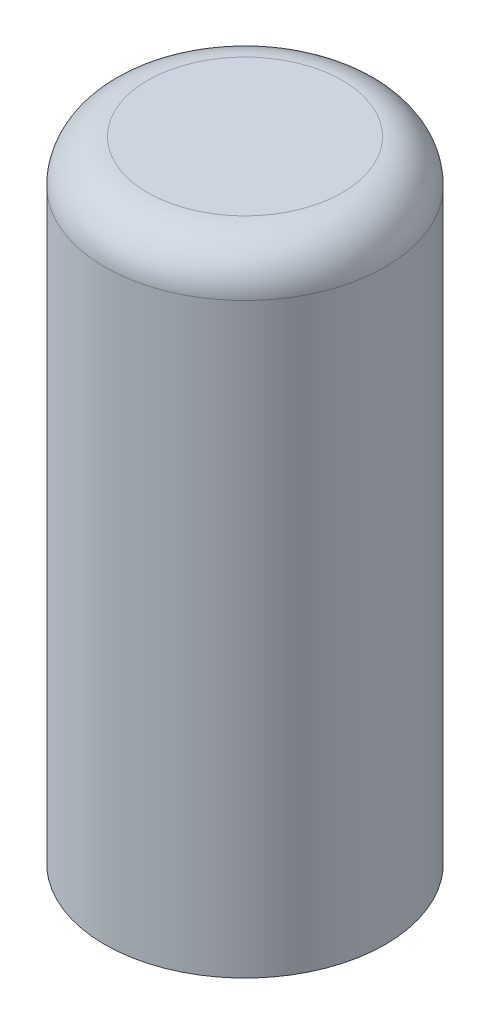
SolidWorks part; units mm, degrees
ref_plane "Front Plane" through (0, 0, 0) normal (0, 0, 1) x (1, 0, 0)
ref_plane "Top Plane" through (0, 0, 0) normal (0, 1, 0) x (1, 0, 0)
ref_plane "Right Plane" through (0, 0, 0) normal (1, 0, 0) x (0, 0, -1)
sketch "Sketch1" plane through (0, 0, 0) normal (0, 1, 0) x (1, 0, 0)
  circle A0 centre (0, 0) radius 4.9
  dimension "D1" = 9.8
extrude "Boss-Extrude1" add sketch "Sketch1" along normal blind 22
fillet "Fillet1" radius 1.5 1 edges at (0, 22, 4.9)
